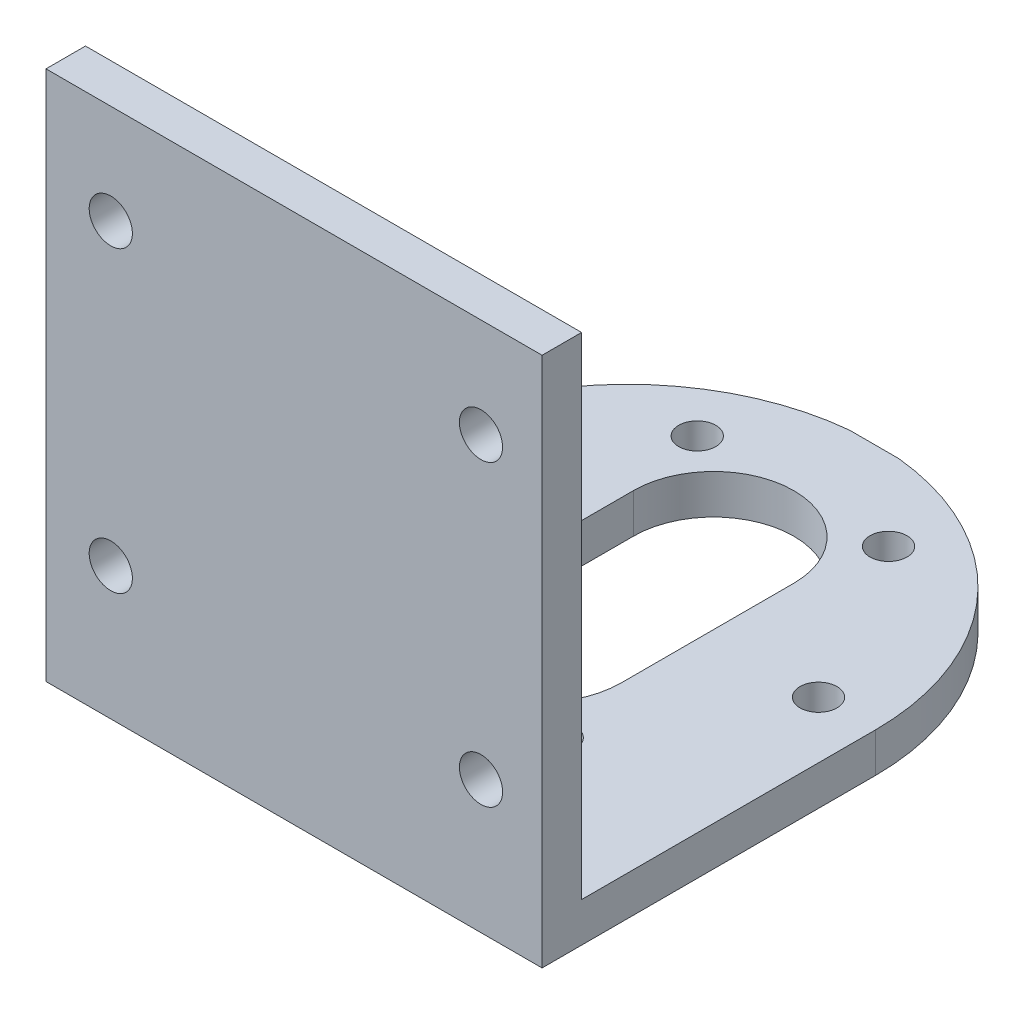
SolidWorks part; units mm, degrees
ref_plane "前视基准面" through (0, 0, 0) normal (0, 0, 1) x (1, 0, 0)
ref_plane "上视基准面" through (0, 0, 0) normal (0, 1, 0) x (1, 0, 0)
ref_plane "右视基准面" through (0, 0, 0) normal (1, 0, 0) x (0, 0, -1)
sketch "草图1" plane through (0, 0, 0) normal (0, 0, 1) x (1, 0, 0)
  line L0 (0, 0) -> (281.0314, 0) construction
  line L1 (0, 0) -> (0, -271.9168) construction
  line L2 (40.2, 3.2) -> (0, 3.2)
  line L3 (0, 0) -> (40.2, 0)
  line L4 (0, 0) -> (0, 43)
  line L5 (0, 43) -> (40.2, 43)
  line L6 (40.2, 0) -> (40.2, 43)
  circle A0 centre (5.25, 34.95) radius 1.75
  circle A1 centre (5.25, 10.75) radius 1.75
  circle A2 centre (35.25, 10.75) radius 1.75
  circle A3 centre (35.25, 34.95) radius 1.75
  dimension "D3" = 8.05
  dimension "D5" = 3.5
  dimension "D6" = 3.5
  dimension "D12" = 3.5
  dimension "D13" = 3.5
  dimension "D1" = 43
  dimension "D2" = 40.2
  dimension "D4" = 5.25
  dimension "D7" = 24.2
  dimension "D8" = 5.25
  dimension "D9" = 3.2
  dimension "D10" = 30
  dimension "D11" = 30
  dimension "D14" = 4.95
  dimension "D15" = 24.2
extrude "凸台-拉伸1" add sketch "草图1" along normal blind 3.2 contours L2 L6 L5 L4 A2 A1 A0 A3 | L3 L6 L2 L4
sketch "草图2" plane through (0, 0, 0) normal (0, 0, -1) x (-1, 0, 0)
  line L0 (0, 0) -> (0, 43) construction
  line L1 (-40.2, 0) -> (0, 0)
  line L2 (-40.2, 0) -> (-40.2, 3.2)
  line L3 (-40.2, 3.2) -> (0, 3.2)
  line L4 (0, 0) -> (0, 3.2)
  dimension "D1" = 3.2
extrude "凸台-拉伸2" add sketch "草图2" along normal blind 43.8
sketch "草图3" plane through (0, 0, 0) normal (0, -1, 0) x (1, 0, 0)
  line L0 (13.6, -30.8) -> (13.6, -16.8)
  line L1 (26.6, -16.8) -> (26.6, -30.8)
  line L2 (0, 3.2) -> (40.2, 3.2) construction
  line L3 (20.1, -30.8) -> (20.1, -16.8)
  line L4 (20.1, -23.8) -> (-5.5239, -23.8)
  line L6 (40.2, 3.2) -> (40.2, -43.8) construction
  arc A0 (13.6, -30.8) -> (26.6, -30.8) centre (20.1, -30.8) ccw
  arc A1 (26.6, -16.8) -> (13.6, -16.8) centre (20.1, -16.8) ccw
  circle A2 centre (4.6, -23.8) radius 1.5
  circle A3 centre (4.6, -23.8) radius 3.0285
  circle A4 centre (12.35, -10.3766) radius 1.5
  circle A5 centre (12.35, -10.3766) radius 3.0285
  circle A6 centre (27.85, -10.3766) radius 1.5
  circle A7 centre (27.85, -10.3766) radius 3.0285
  circle A8 centre (35.6, -23.8) radius 1.5
  circle A9 centre (35.6, -23.8) radius 3.0285
  circle A10 centre (27.85, -37.2234) radius 1.5
  circle A11 centre (27.85, -37.2234) radius 3.0285
  circle A12 centre (12.35, -37.2234) radius 1.5
  circle A13 centre (12.35, -37.2234) radius 3.0285
  point P16 (0, 0)
  point P32 (20.1, -23.8)
  dimension "D1" = 13
  dimension "D2" = 13
  dimension "D5" = 3
  dimension "D6" = 6.0571
  dimension "D3" = 34
  dimension "D4" = 20
  dimension "D7" = 20.1
  dimension "D8" = 15.5
  dimension "D9" = 6
extrude "切除-拉伸1" cut sketch "草图3" against normal through all
sketch "草图4" plane through (0, 0, 0) normal (0, -1, 0) x (1, 0, 0)
  line L0 (13.6, -30.8) -> (13.6, -16.8)
  line L1 (26.6, -16.8) -> (26.6, -30.8)
  line L2 (20.1, -30.8) -> (20.1, -16.8)
  line L3 (20.1, -23.8) -> (-5.5239, -23.8)
  arc A0 (13.6, -30.8) -> (26.6, -30.8) centre (20.1, -30.8) ccw
  arc A1 (26.6, -16.8) -> (13.6, -16.8) centre (20.1, -16.8) ccw
  circle A2 centre (4.6, -23.8) radius 1.5
  circle A3 centre (4.6, -23.8) radius 3.0285
  circle A4 centre (12.35, -10.3766) radius 1.5
  circle A5 centre (12.35, -10.3766) radius 3.0285
  circle A6 centre (27.85, -10.3766) radius 1.5
  circle A7 centre (27.85, -10.3766) radius 3.0285
  circle A8 centre (35.6, -23.8) radius 1.5
  circle A9 centre (35.6, -23.8) radius 3.0285
  circle A10 centre (27.85, -37.2234) radius 1.5
  circle A11 centre (27.85, -37.2234) radius 3.0285
  circle A12 centre (12.35, -37.2234) radius 1.5
  circle A13 centre (12.35, -37.2234) radius 3.0285
  point P26 (20.1, -23.8)
  circle M7 centre (12.35, -37.2234) radius 1.5
  circle M9 centre (35.6, -23.8) radius 1.5
  circle M10 centre (27.85, -37.2234) radius 1.5
extrude "切除-拉伸2" cut sketch "草图4" against normal blind 1 contours A11 M10 | A13 M7 | A9 M9 | A7 A6 | A3 | A5
sketch "草图5" plane through (0, 0, 0) normal (0, -1, 0) x (1, 0, 0)
  line L0 (13.6, -30.8) -> (13.6, -16.8)
  line L1 (26.6, -16.8) -> (26.6, -30.8)
  line L2 (20.1, -30.8) -> (20.1, -16.8)
  line L3 (20.1, -23.8) -> (-5.5239, -23.8)
  line L4 (0, -23.8) -> (0, -43.8)
  line L5 (0, -43.8) -> (20.1, -43.9)
  line L6 (20.1, -43.9) -> (40.2, -43.8)
  line L7 (40.2, -43.8) -> (40.2, -23.8)
  arc A0 (13.6, -30.8) -> (26.6, -30.8) centre (20.1, -30.8) ccw
  arc A1 (26.6, -16.8) -> (13.6, -16.8) centre (20.1, -16.8) ccw
  circle A2 centre (4.6, -23.8) radius 1.5
  circle A3 centre (4.6, -23.8) radius 3.0285
  circle A4 centre (12.35, -10.3766) radius 1.5
  circle A5 centre (12.35, -10.3766) radius 3.0285
  circle A6 centre (27.85, -10.3766) radius 1.5
  circle A7 centre (27.85, -10.3766) radius 3.0285
  circle A8 centre (35.6, -23.8) radius 1.5
  circle A9 centre (35.6, -23.8) radius 3.0285
  circle A10 centre (27.85, -37.2234) radius 1.5
  circle A11 centre (27.85, -37.2234) radius 3.0285
  circle A12 centre (12.35, -37.2234) radius 1.5
  circle A13 centre (12.35, -37.2234) radius 3.0285
  circle A14 centre (20.1, -23.8) radius 20.1
  point P26 (20.1, -23.8)
  line M17 (0, 3.2) -> (0, -43.8)
  line M18 (0, -43.8) -> (40.2, -43.8)
  line M19 (40.2, -43.8) -> (40.2, 3.2)
extrude "切除-拉伸3" cut sketch "草图5" against normal through all contours A14 M17 M18 | A14 M18 M19
